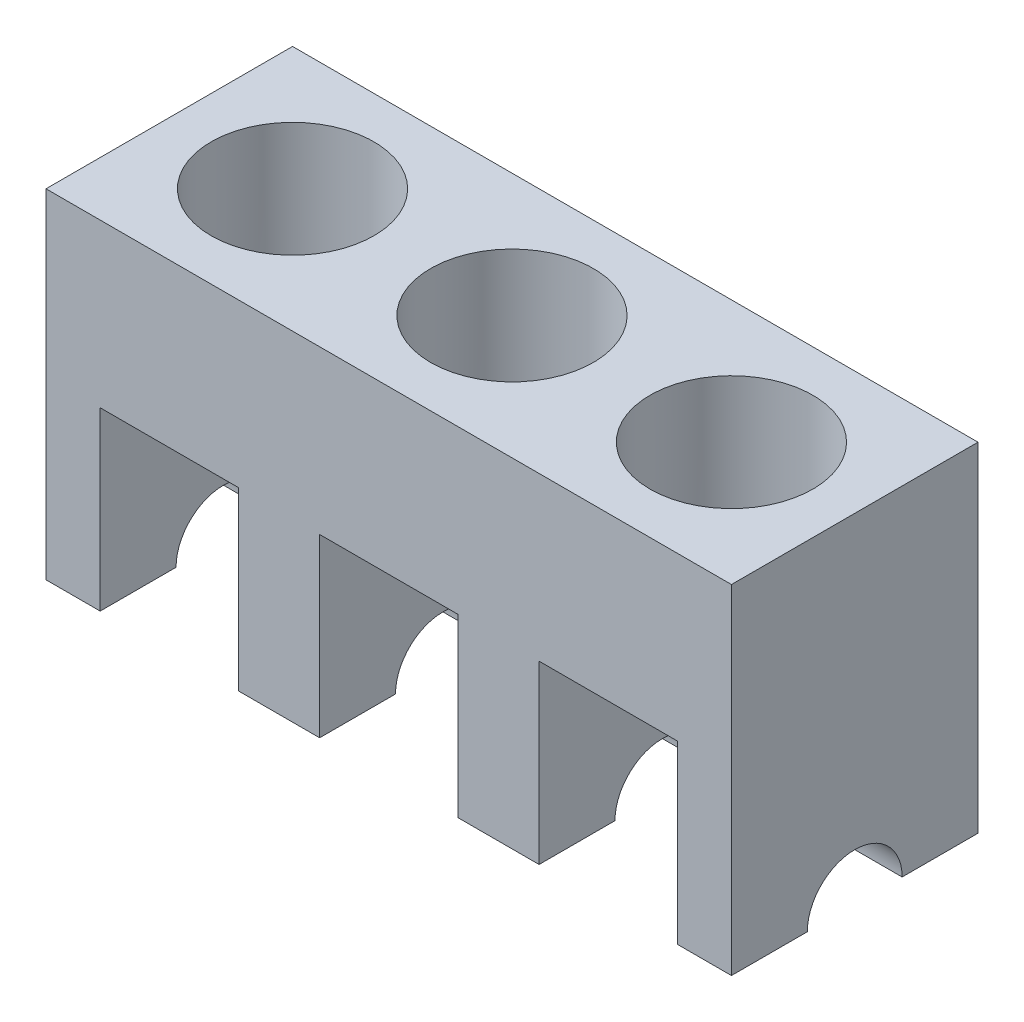
SolidWorks part; units mm, degrees
material "3003 Alloy"
ref_plane "Front Plane" through (0, 0, 0) normal (0, 0, 1) x (1, 0, 0)
ref_plane "Top Plane" through (0, 0, 0) normal (0, 1, 0) x (1, 0, 0)
ref_plane "Right Plane" through (0, 0, 0) normal (1, 0, 0) x (0, 0, -1)
sketch "Sketch1" plane through (0, 0, 0) normal (0, 1, 0) x (1, 0, 0)
  line L0 (0, 0) -> (0, -91)
  line L1 (0, -91) -> (253, -91)
  line L2 (253, -91) -> (253, 0)
  line L3 (253, 0) -> (0, 0)
  dimension "D1" = 253
  dimension "D2" = 91
extrude "Boss-Extrude1" add sketch "Sketch1" along normal blind 125
sketch "Sketch2" plane through (0, 0, 91) normal (0, 0, 1) x (1, 0, 0)
  line L0 (0, 0) -> (20, 0) construction
  line L1 (50.05, 0) -> (-50.05, 0) construction
  line L2 (20, 0) -> (20, 65)
  line L3 (20, 65) -> (71, 65)
  line L4 (71, 65) -> (71, 0)
  line L5 (71, 0) -> (20, 0)
  line L6 (71, 0) -> (101, 0) construction
  line L7 (101, 0) -> (101, 65)
  line L8 (101, 65) -> (152, 65)
  line L9 (152, 65) -> (152, 0)
  line L10 (152, 0) -> (101, 0)
  line L11 (152, 0) -> (182, 0) construction
  line L12 (182, 0) -> (182, 65)
  line L13 (182, 65) -> (233, 65)
  line L14 (233, 65) -> (233, 0)
  line L15 (233, 0) -> (182, 0)
  line L16 (233, 0) -> (253, 0) construction
  line L17 (253, 125) -> (253, 0) construction
  line L18 (0, 125) -> (0, 0) construction
  dimension "D1" = 51
  dimension "D2" = 65
  dimension "D3" = 65
  dimension "D4" = 51
  dimension "D5" = 65
  dimension "D6" = 51
  dimension "D7" = 30
  dimension "D8" = 30
  dimension "D9" = 20
extrude "Cut-Extrude1" cut sketch "Sketch2" against normal through all
sketch "Sketch3" plane through (0, 125, 0) normal (0, 1, 0) x (1, 0, 0)
  line L0 (0, -45.5) -> (45.5, -45.5) construction
  line L1 (0, 0) -> (0, -91) construction
  line L2 (45.5, -45.5) -> (126.5, -45.5) construction
  line L3 (126.5, -45.5) -> (207.5, -45.5) construction
  circle A0 centre (45.5, -45.5) radius 30.05
  circle A1 centre (126.5, -45.5) radius 30.05
  circle A2 centre (207.5, -45.5) radius 30.05
  dimension "D1" = 45.5
  dimension "D4" = 60.1
  dimension "D5" = 60.1
  dimension "D6" = 60.1
  dimension "D2" = 81
  dimension "D3" = 81
extrude "Cut-Extrude2" cut sketch "Sketch3" against normal blind 81
sketch "Sketch4" plane through (253, 0, 0) normal (1, 0, 0) x (0, 0, -1)
  line L0 (-45.5, 125) -> (-45.5, 0) construction
  line L1 (-91, 125) -> (0, 125) construction
  line L2 (50.05, 0) -> (-50.05, 0) construction
  circle A0 centre (-45.5, 0) radius 17.5
  dimension "D1" = 35
extrude "Cut-Extrude3" cut sketch "Sketch4" against normal through all
